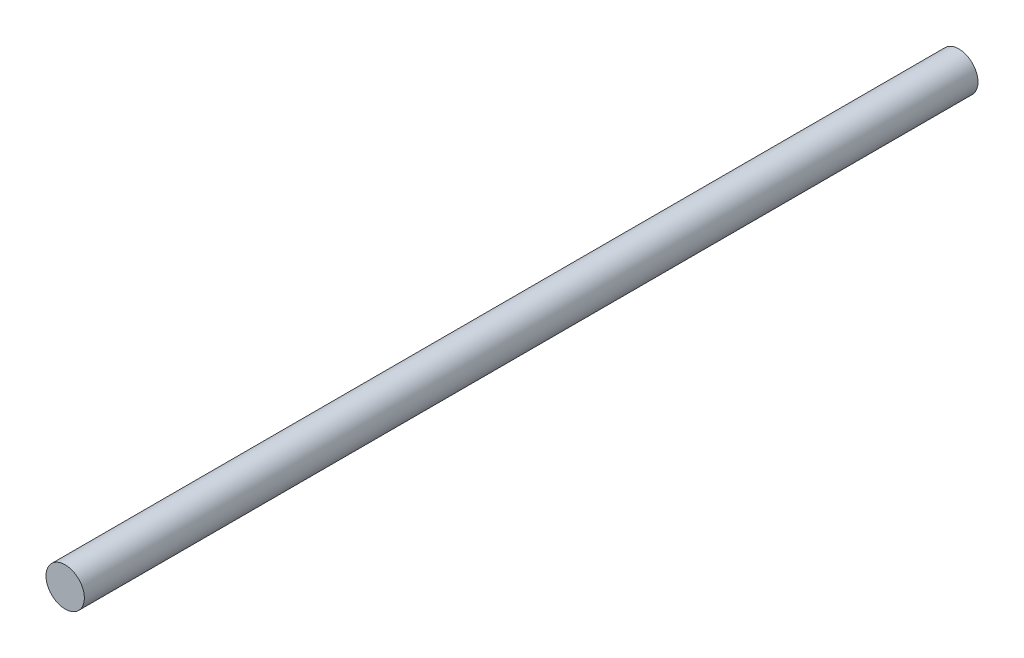
SolidWorks part; units mm, degrees
ref_plane "Спереди" through (0, 0, 0) normal (0, 0, 1) x (1, 0, 0)
ref_plane "Сверху" through (0, 0, 0) normal (0, 1, 0) x (1, 0, 0)
ref_plane "Справа" through (0, 0, 0) normal (1, 0, 0) x (0, 0, -1)
sketch "Эскиз1" plane through (0, 0, 0) normal (0, 0, 1) x (1, 0, 0)
  circle A0 centre (0, 0) radius 10.75
  dimension "D1" = 21.5
extrude "Бобышка-Вытянуть1" add sketch "Эскиз1" along normal blind 500.5
